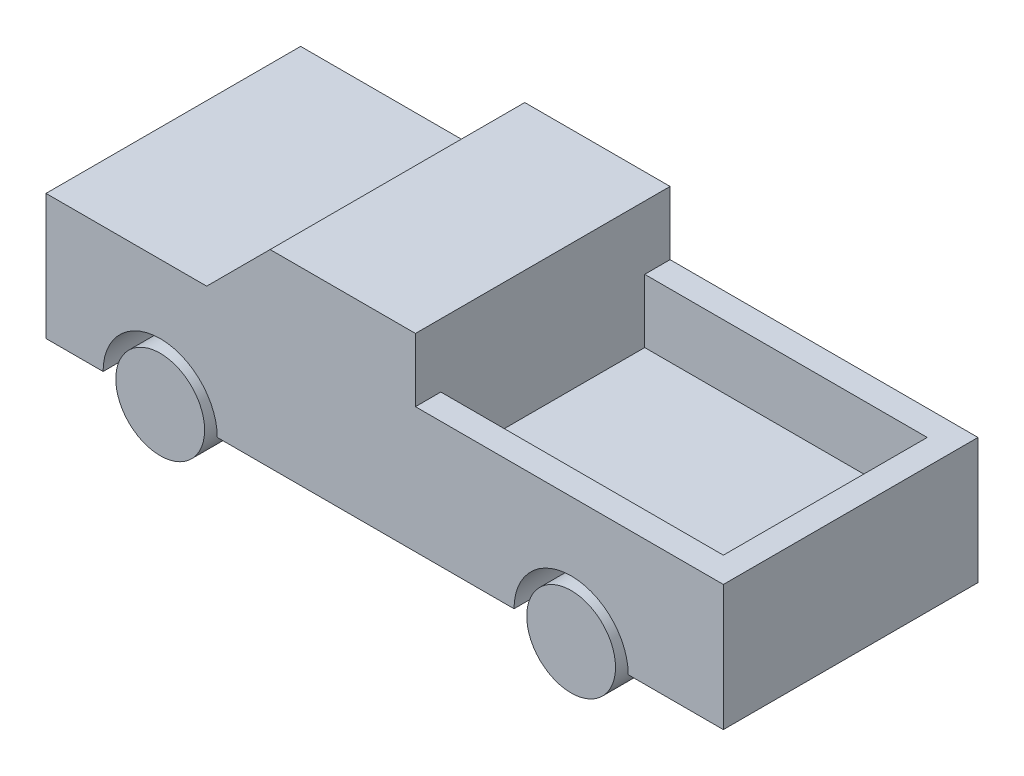
SolidWorks part; units mm, degrees
ref_plane "Front Plane" through (0, 0, 0) normal (0, 0, 1) x (1, 0, 0)
ref_plane "Top Plane" through (0, 0, 0) normal (0, 1, 0) x (1, 0, 0)
ref_plane "Right Plane" through (0, 0, 0) normal (1, 0, 0) x (0, 0, -1)
sketch "Sketch1" plane through (0, 0, 0) normal (0, 0, 1) x (1, 0, 0)
  line L0 (1266.5035, -500) -> (1766.5035, 0)
  line L1 (1766.5035, 0) -> (2911.9969, 0)
  line L2 (0, -500) -> (0, -1491)
  line L4 (5339, -500) -> (5339, -1491)
  line L5 (0, -500) -> (1266.5035, -500)
  line L6 (0, -500) -> (0, -1491)
  line L7 (0, -1491) -> (450, -1491)
  line L8 (5339, -500) -> (5339, -1491)
  line L9 (2911.9969, 0) -> (2911.9969, -500)
  line L10 (2911.9969, -500) -> (5339, -500)
  line L12 (1350, -1491) -> (3689, -1491)
  line L14 (4589, -1491) -> (5339, -1491)
  circle A0 centre (900, -1491) radius 350
  circle A1 centre (4139, -1491) radius 350
  arc A2 (1350, -1491) -> (450, -1491) centre (900, -1491) ccw
  arc A3 (4589, -1491) -> (3689, -1491) centre (4139, -1491) ccw
  dimension "D3" = 700
  dimension "D4" = 700
  dimension "D7" = 900
  dimension "D8" = 900
  dimension "D5" = 900
  dimension "D6" = 1200
  dimension "D10" = 500
extrude "Boss-Extrude1" add sketch "Sketch1" along normal blind 2007 contours A3 L14 L4 L10 L9 L1 L0 L5 L2 L7 A2 L12 | A0 | A1
sketch "Sketch2" plane through (0, -500, 0) normal (0, 1, 0) x (1, 0, 0)
  line L0 (2911.9969, -2007) -> (2911.9969, 0) construction
  line L1 (2911.9969, -200) -> (5139, -200)
  line L2 (2911.9969, -200) -> (2911.9969, -1807)
  line L3 (2911.9969, -1807) -> (5139, -1807)
  line L4 (5139, -200) -> (5139, -1807)
  line L5 (2911.9969, 0) -> (5339, 0) construction
  line L6 (5339, -2007) -> (5339, 0) construction
  line L7 (2911.9969, -2007) -> (5339, -2007) construction
  dimension "D1" = 200
  dimension "D2" = 200
  dimension "D3" = 200
extrude "Cut-Extrude1" cut sketch "Sketch2" against normal blind 500
